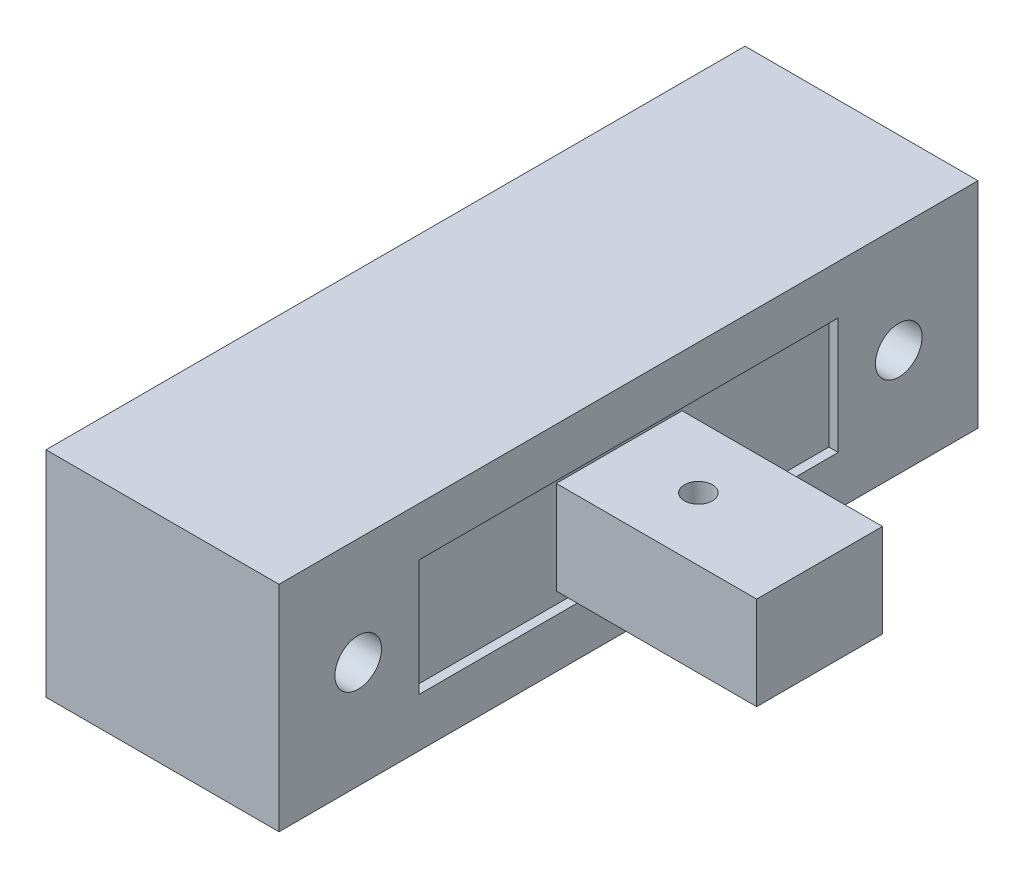
SolidWorks part; units mm, degrees
ref_plane "前视基准面" through (0, 0, 0) normal (0, 0, 1) x (1, 0, 0)
ref_plane "上视基准面" through (0, 0, 0) normal (0, 1, 0) x (1, 0, 0)
ref_plane "右视基准面" through (0, 0, 0) normal (1, 0, 0) x (0, 0, -1)
sketch "草图1" plane through (0, 0, 0) normal (0, 1, 0) x (1, 0, 0)
  line L1 (-5, -15) -> (5, -15)
  line L2 (-5, -15) -> (-5, 15)
  line L3 (-5, 15) -> (5, 15)
  line L4 (5, -15) -> (5, 15)
  line L5 (-5, -15) -> (5, 15) construction
  line L6 (-5, 15) -> (5, -15) construction
  point P0 (0, 0)
  dimension "D1" = 10
  dimension "D2" = 30
extrude "凸台-拉伸1" add sketch "草图1" along normal mid plane 9.2
sketch "草图2" plane through (5, 0, 0) normal (1, 0, 0) x (0, 0, -1)
  line L1 (-9, -2.5) -> (9, -2.5)
  line L2 (-9, -2.5) -> (-9, 2.5)
  line L3 (-9, 2.5) -> (9, 2.5)
  line L4 (9, -2.5) -> (9, 2.5)
  line L5 (-9, -2.5) -> (9, 2.5) construction
  line L6 (-9, 2.5) -> (9, -2.5) construction
  point P0 (0, 0)
  dimension "D1" = 18
  dimension "D2" = 5
extrude "切除-拉伸1" cut sketch "草图2" against normal blind 0.4
sketch "草图3" plane through (4.6, 0, 0) normal (1, 0, 0) x (0, 0, -1)
  line L1 (-2.7, -2) -> (2.7, -2)
  line L2 (-2.7, -2) -> (-2.7, 2)
  line L3 (-2.7, 2) -> (2.7, 2)
  line L4 (2.7, -2) -> (2.7, 2)
  line L5 (-2.7, -2) -> (2.7, 2) construction
  line L6 (-2.7, 2) -> (2.7, -2) construction
  point P0 (0, 0)
  dimension "D1" = 5.4
  dimension "D2" = 4
extrude "凸台-拉伸2" add sketch "草图3" along normal blind 8.6
sketch "草图4" plane through (0, 2, 0) normal (0, 1, 0) x (1, 0, 0)
  circle A0 centre (8, 0) radius 0.6
  dimension "D1" = 1.2
  dimension "D2" = 8
extrude "切除-拉伸2" cut sketch "草图4" against normal blind 4
sketch "草图5" plane through (5, 0, 0) normal (1, 0, 0) x (0, 0, -1)
  circle A0 centre (11.6, 0) radius 1
  circle A1 centre (-11.6, 0) radius 1
  dimension "D1" = 2
  dimension "D2" = 2
  dimension "D3" = 23.2
  dimension "D4" = 11.6
extrude "切除-拉伸3" cut sketch "草图5" against normal through all
